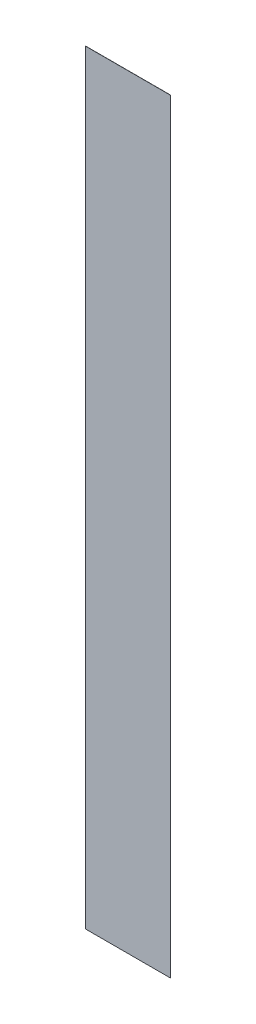
SolidWorks part; units mm, degrees
ref_plane "Front Plane" through (0, 0, 0) normal (0, 0, 1) x (1, 0, 0)
ref_plane "Top Plane" through (0, 0, 0) normal (0, 1, 0) x (1, 0, 0)
ref_plane "Right Plane" through (0, 0, 0) normal (1, 0, 0) x (0, 0, -1)
sketch "Sketch1" plane through (0, 0, 0) normal (0, 0, 1) x (1, 0, 0)
  line L1 (-6.7713, 2.2085) -> (13.2287, 2.2085)
  line L2 (-6.7713, 2.2085) -> (-6.7713, -177.7915)
  line L3 (-6.7713, -177.7915) -> (13.2287, -177.7915)
  line L4 (13.2287, 2.2085) -> (13.2287, -177.7915)
  dimension "D1" = 20
  dimension "D2" = 180
extrude "Boss-Extrude1" add sketch "Sketch1" along normal blind 0.04
